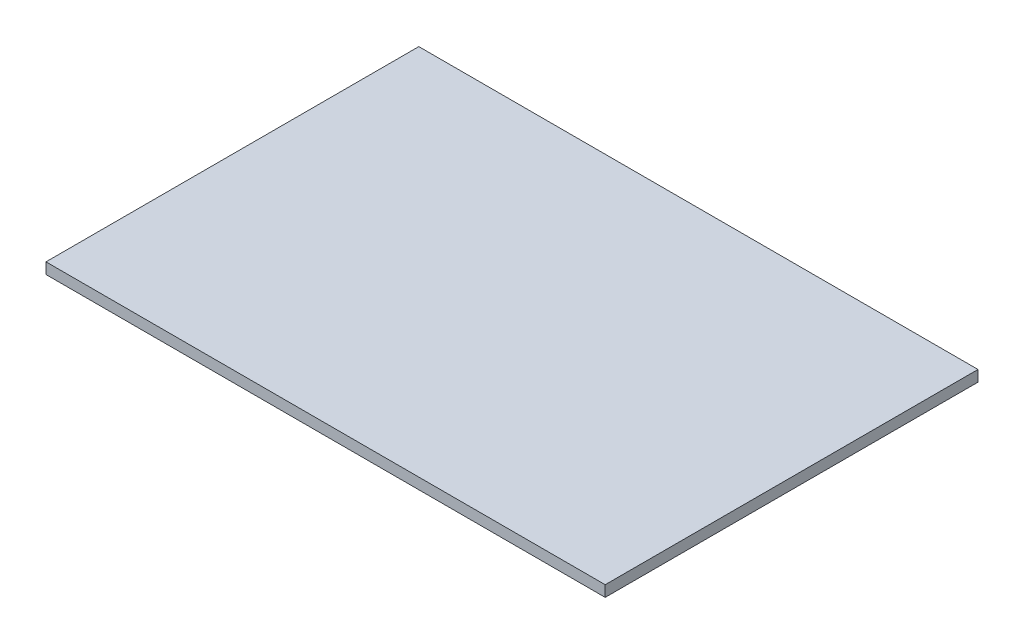
SolidWorks part; units mm, degrees
ref_plane "Front Plane" through (0, 0, 0) normal (0, 0, 1) x (1, 0, 0)
ref_plane "Top Plane" through (0, 0, 0) normal (0, 1, 0) x (1, 0, 0)
ref_plane "Right Plane" through (0, 0, 0) normal (1, 0, 0) x (0, 0, -1)
sketch "Sketch4" plane through (0, 0, 0) normal (0, 1, 0) x (1, 0, 0)
  line L1 (152.4, -101.6) -> (-152.4, -101.6)
  line L2 (152.4, -101.6) -> (152.4, 101.6)
  line L3 (152.4, 101.6) -> (-152.4, 101.6)
  line L4 (-152.4, -101.6) -> (-152.4, 101.6)
  line L5 (152.4, -101.6) -> (-152.4, 101.6) construction
  line L6 (152.4, 101.6) -> (-152.4, -101.6) construction
  point P0 (0, 0)
extrude "Boss-Extrude2" add sketch "Sketch4" along normal blind 6
